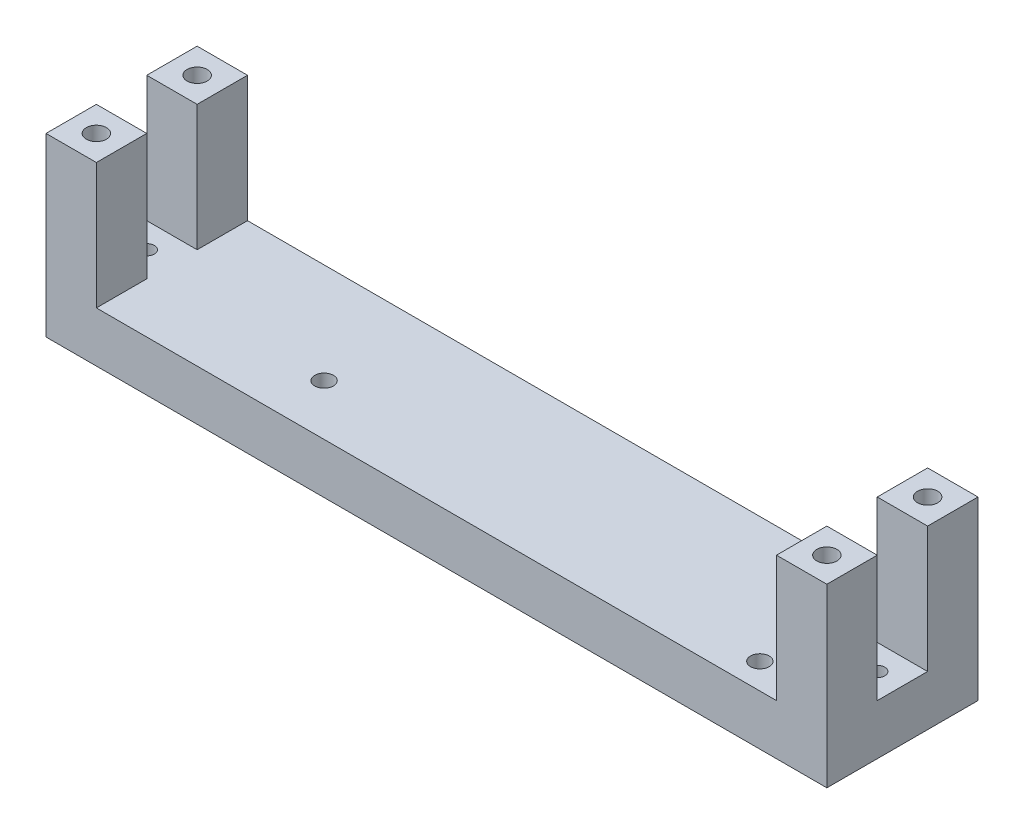
SolidWorks part; units mm, degrees
ref_plane "Front Plane" through (0, 0, 0) normal (0, 0, 1) x (1, 0, 0)
ref_plane "Top Plane" through (0, 0, 0) normal (0, 1, 0) x (1, 0, 0)
ref_plane "Right Plane" through (0, 0, 0) normal (1, 0, 0) x (0, 0, -1)
sketch "Sketch3" plane through (0, 0, 0) normal (0, 1, 0) x (1, 0, 0)
  line L1 (-54.3027, 163.9626) -> (100.6973, 163.9626)
  line L2 (-54.3027, 163.9626) -> (-54.3027, 133.9626)
  line L3 (-54.3027, 133.9626) -> (100.6973, 133.9626)
  line L4 (100.6973, 163.9626) -> (100.6973, 133.9626)
  dimension "D1" = 155
  dimension "D2" = 30
extrude "Boss-Extrude3" add sketch "Sketch3" along normal blind 10
sketch "Sketch4" plane through (0, 10, 0) normal (0, 1, 0) x (1, 0, 0)
  line L1 (-54.3027, 163.9626) -> (-44.3027, 163.9626)
  line L2 (-54.3027, 163.9626) -> (-54.3027, 153.9626)
  line L3 (-54.3027, 153.9626) -> (-44.3027, 153.9626)
  line L4 (-44.3027, 163.9626) -> (-44.3027, 153.9626)
  line L5 (-54.3027, 133.9626) -> (-44.3027, 133.9626)
  line L6 (-54.3027, 133.9626) -> (-54.3027, 143.9626)
  line L7 (-54.3027, 143.9626) -> (-44.3027, 143.9626)
  line L8 (-44.3027, 133.9626) -> (-44.3027, 143.9626)
  line L9 (100.6973, 163.9626) -> (90.6973, 163.9626)
  line L10 (100.6973, 163.9626) -> (100.6973, 153.9626)
  line L11 (100.6973, 153.9626) -> (90.6973, 153.9626)
  line L12 (90.6973, 163.9626) -> (90.6973, 153.9626)
  line L13 (100.6973, 133.9626) -> (90.6973, 133.9626)
  line L14 (100.6973, 133.9626) -> (100.6973, 143.9626)
  line L15 (100.6973, 143.9626) -> (90.6973, 143.9626)
  line L16 (90.6973, 133.9626) -> (90.6973, 143.9626)
  dimension "D1" = 10
  dimension "D2" = 10
  dimension "D3" = 10
  dimension "D4" = 10
  dimension "D5" = 10
  dimension "D6" = 10
  dimension "D7" = 10
  dimension "D8" = 10
extrude "Boss-Extrude4" add sketch "Sketch4" along normal blind 25
sketch "Sketch6" plane through (0, 35, 0) normal (0, 1, 0) x (1, 0, 0)
  line L0 (100.6973, 163.9626) -> (90.6973, 163.9626) construction
  line L1 (100.6973, 153.9626) -> (100.6973, 163.9626) construction
  line L2 (100.6973, 133.9626) -> (100.6973, 143.9626) construction
  line L3 (90.6973, 133.9626) -> (100.6973, 133.9626) construction
  line L4 (-54.3027, 133.9626) -> (-44.3027, 133.9626) construction
  line L5 (-54.3027, 143.9626) -> (-54.3027, 133.9626) construction
  line L6 (-54.3027, 163.9626) -> (-54.3027, 153.9626) construction
  line L7 (-44.3027, 163.9626) -> (-54.3027, 163.9626) construction
  circle A0 centre (95.6973, 138.9626) radius 2
  circle A1 centre (95.6973, 158.9626) radius 2
  circle A2 centre (-49.3027, 138.9626) radius 2
  circle A3 centre (-49.3027, 158.9626) radius 2
  dimension "D1" = 4
  dimension "D2" = 4
  dimension "D3" = 4
  dimension "D4" = 4
  dimension "D8" = 5
  dimension "D5" = 5
  dimension "D6" = 5
  dimension "D7" = 5
  dimension "D9" = 5
  dimension "D10" = 5
  dimension "D11" = 5
  dimension "D12" = 5
extrude "Cut-Extrude1" cut sketch "Sketch6" against normal blind 10
sketch "Sketch7" plane through (0, 10, 0) normal (0, 1, 0) x (1, 0, 0)
  line L0 (100.6973, 143.9626) -> (100.6973, 153.9626) construction
  line L1 (100.6973, 163.9626) -> (90.6973, 163.9626) construction
  line L2 (-54.3027, 133.9626) -> (-44.3027, 133.9626) construction
  line L3 (-54.3027, 153.9626) -> (-54.3027, 143.9626) construction
  line L4 (100.6973, 133.9626) -> (100.6973, 143.9626) construction
  line L5 (100.6973, 153.9626) -> (100.6973, 163.9626) construction
  line L6 (90.6973, 163.9626) -> (-44.3027, 163.9626) construction
  circle A0 centre (95.6973, 148.9626) radius 1.5
  circle A1 centre (82.2973, 139.0626) radius 1.85
  circle A2 centre (82.2973, 159.0626) radius 1.85
  circle A3 centre (-49.3027, 148.9626) radius 1.5
  circle A4 centre (-9.2027, 144.0626) radius 1.85
  dimension "D1" = 3
  dimension "D2" = 3
  dimension "D3" = 3.7
  dimension "D4" = 3.7
  dimension "D5" = 3.7
  dimension "D6" = 5
  dimension "D7" = 15
  dimension "D8" = 15
  dimension "D9" = 5
  dimension "D10" = 18.4
  dimension "D11" = 18.4
  dimension "D12" = 4.9
  dimension "D13" = 24.9
  dimension "D14" = 109.9
  dimension "D15" = 19.9
extrude "Cut-Extrude2" cut sketch "Sketch7" against normal blind 10
